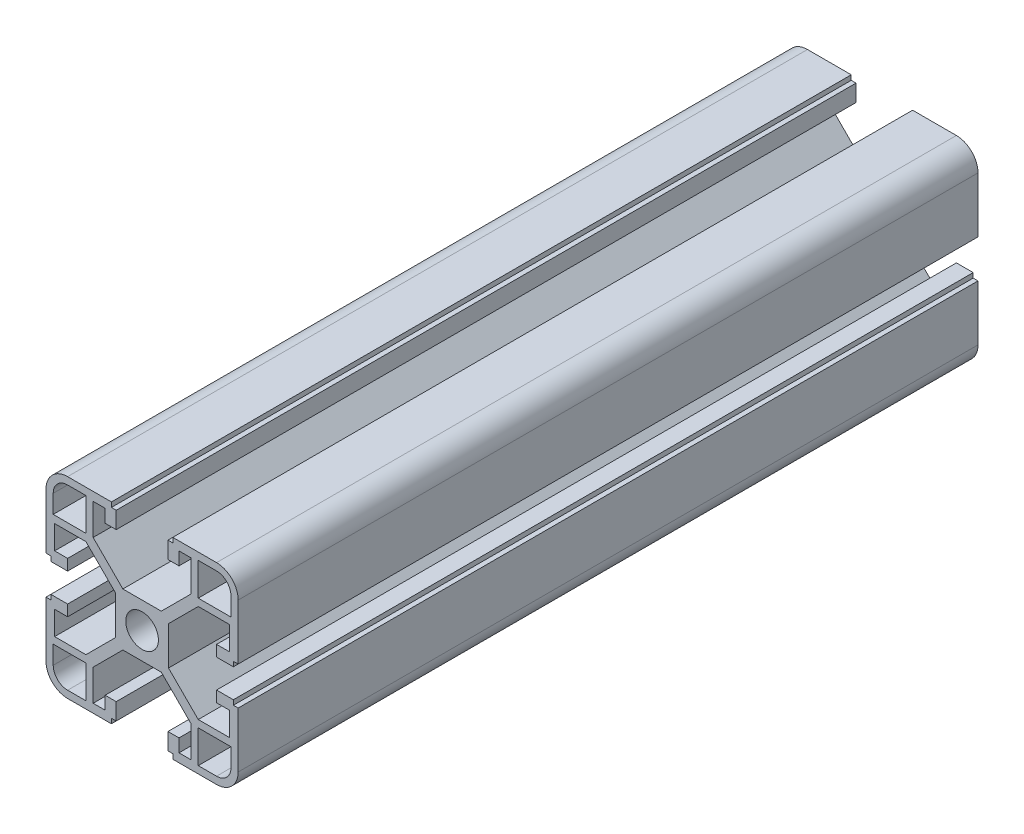
SolidWorks part; units mm, degrees
material "6061-T6 (SS)"
ref_plane "Front Plane" through (0, 0, 0) normal (0, 0, 1) x (1, 0, 0)
ref_plane "Top Plane" through (0, 0, 0) normal (0, 1, 0) x (1, 0, 0)
ref_plane "Right Plane" through (0, 0, 0) normal (1, 0, 0) x (0, 0, -1)
sketch "Sketch1" plane through (0, 0, 0) normal (0, 0, 1) x (1, 0, 0)
  line L0 (3.4, 0) -> (5.5, 0)
  line L1 (10.19, 11.69) -> (4, 5.5)
  line L2 (11.69, 10.19) -> (5.5, 4)
  line L3 (18.2, 10.19) -> (11.69, 10.19)
  line L4 (18.2, 10.19) -> (18.2, 5.2656)
  line L5 (18.2, 5.2656) -> (15.5, 5.2656)
  line L6 (15.5, 5.2656) -> (15.5, 2.9656)
  line L7 (15.5, 2.9656) -> (19, 2.9656)
  line L8 (19, 2.9656) -> (19, 3.9656)
  line L9 (19, 3.9656) -> (20, 3.9656)
  line L10 (20, 3.9656) -> (20, 15.5)
  line L11 (15.5, 20) -> (6.3853, 20)
  line L12 (18.5, 11.69) -> (18.5, 15.5)
  line L13 (15.5, 18.5) -> (11.69, 18.5)
  line L14 (11.69, 11.69) -> (11.69, 18.5)
  line L15 (0, 3.4) -> (0, 5.5)
  line L16 (4, 5.5) -> (0, 5.5)
  line L17 (6.3853, 20) -> (6.3853, 19)
  line L18 (5.5, 0) -> (5.5, 4)
  line L19 (6.3853, 19) -> (5.3853, 19)
  line L20 (5.3853, 19) -> (5.3853, 15.5)
  line L21 (5.3853, 15.5) -> (7.6853, 15.5)
  line L22 (10.19, 11.69) -> (10.19, 18.2)
  line L23 (11.69, 11.69) -> (18.5, 11.69)
  line L24 (7.6853, 18.2) -> (7.6853, 15.5)
  line L25 (10.19, 18.2) -> (7.6853, 18.2)
  arc A0 (20, 15.5) -> (15.5, 20) centre (15.5, 15.5) ccw
  arc A1 (18.5, 15.5) -> (15.5, 18.5) centre (15.5, 15.5) ccw
  arc A2 (3.4, 0) -> (0, 3.4) centre (0, 0) ccw
  dimension "D3" = 4.5
  dimension "D18" = 1.5
  dimension "D9" = 3.4
  dimension "D20" = 1.8
  dimension "D25" = 3
  dimension "D1" = 5.5
  dimension "D2" = 1.5
  dimension "D4" = 14.5
  dimension "D5" = 1.5
  dimension "D6" = 2.1
  dimension "D7" = 2.3
  dimension "D8" = 1.8
  dimension "D10" = 6.81
  dimension "D11" = 2.1
  dimension "D12" = 1
  dimension "D13" = 4.5
  dimension "D14" = 45
  dimension "D15" = 14.5
  dimension "D16" = 1
  dimension "D17" = 1.5
  dimension "D19" = 6.81
  dimension "D21" = 4.5
  dimension "D22" = 2.3
  dimension "D23" = 1
  dimension "D24" = 1
  dimension "D26" = 8.754
  dimension "D27" = 8.754
  dimension "D28" = 4.9244
  dimension "D29" = 2.5047
extrude "Boss-Extrude1" add sketch "Sketch1" along normal blind 154
mirror "Mirror1" about plane through (0, 0, 0) normal (0, 1, 0) of "Boss-Extrude1"
mirror "Mirror2" about plane through (0, 0, 0) normal (1, 0, 0) of "Boss-Extrude1"
mirror "Mirror3" about plane through (0, 0, 0) normal (0, 1, 0) of "Mirror2"
